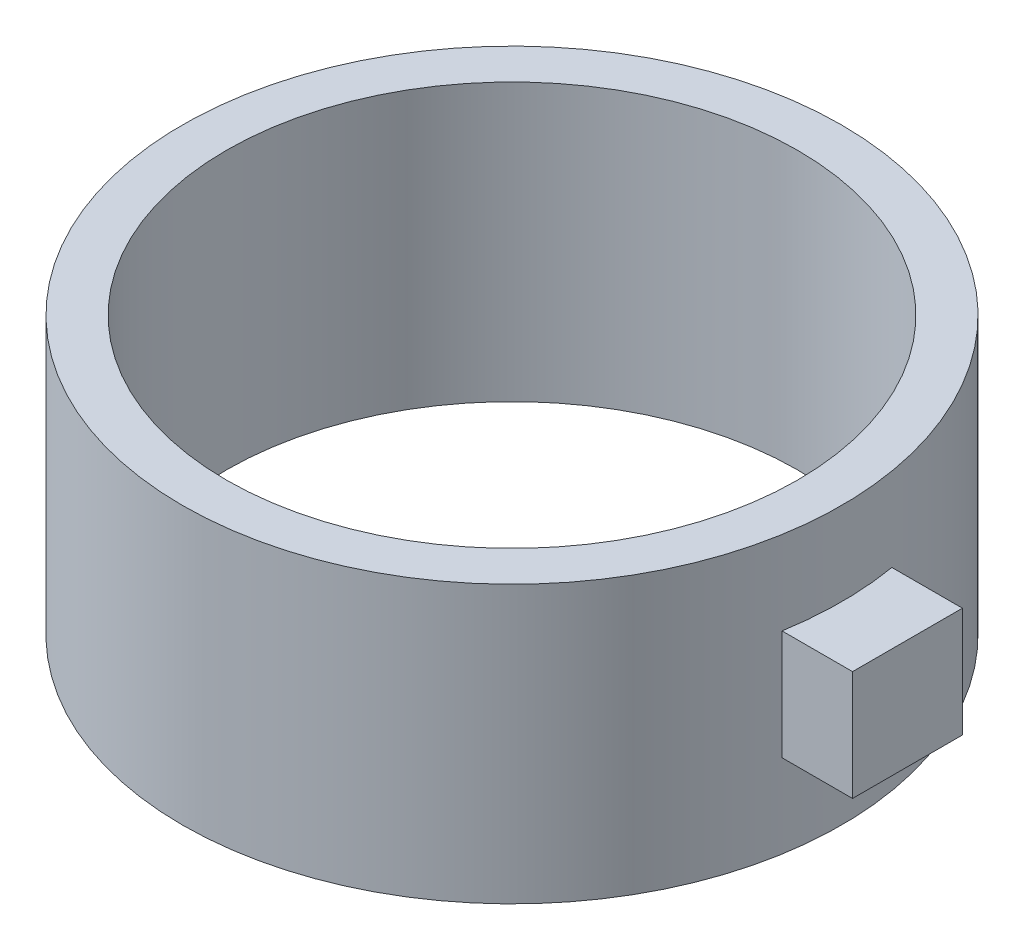
SolidWorks part; units mm, degrees
ref_plane "Front Plane" through (0, 0, 0) normal (0, 0, 1) x (1, 0, 0)
ref_plane "Top Plane" through (0, 0, 0) normal (0, 1, 0) x (1, 0, 0)
ref_plane "Right Plane" through (0, 0, 0) normal (1, 0, 0) x (0, 0, -1)
sketch "Sketch1" plane through (0, 0, 0) normal (0, 1, 0) x (1, 0, 0)
  circle A0 centre (2.5436, -2.5436) radius 15
  circle A1 centre (2.5436, -2.5436) radius 13
extrude "Boss-Extrude2" add sketch "Sketch1" along normal blind 12.6 contours A0 | A1
ref_plane "Plane2" through (17.5436, 0, 0) normal (1, 0, 0) x (0, 0, -1)
sketch "Sketch3" plane through (17.5436, 0, 0) normal (1, 0, 0) x (0, 0, -1)
  line L6 (-5.0436, 6.3) -> (-5.0436, 8.8)
  line L7 (-5.0436, 6.3) -> (-5.0436, 3.8)
  line L8 (-0.0436, 6.3) -> (-0.0436, 8.8)
  line L9 (-0.0436, 6.3) -> (-0.0436, 3.8)
  line L10 (-5.0436, 8.8) -> (-0.0436, 8.8)
  line L11 (-0.0436, 3.8) -> (-5.0436, 3.8)
extrude "Boss-Extrude3" add sketch "Sketch3" along normal blind 3 and the other way blind 1
